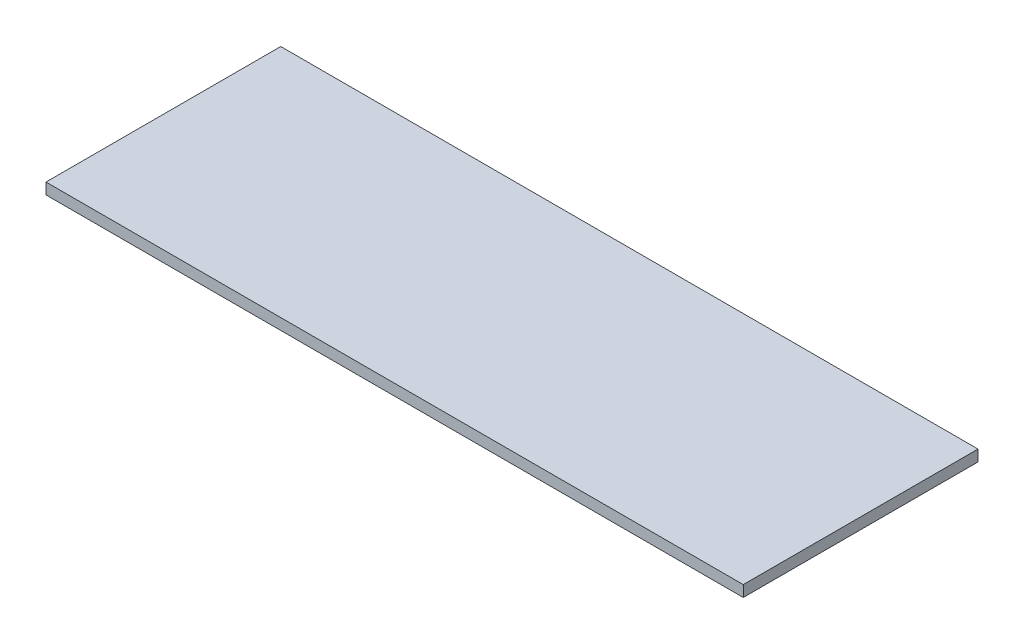
SolidWorks part; units mm, degrees
ref_plane "Front Plane" through (0, 0, 0) normal (0, 0, 1) x (1, 0, 0)
ref_plane "Top Plane" through (0, 0, 0) normal (0, 1, 0) x (1, 0, 0)
ref_plane "Right Plane" through (0, 0, 0) normal (1, 0, 0) x (0, 0, -1)
sketch "Sketch1" plane through (0, 0, 0) normal (0, 1, 0) x (1, 0, 0)
  line L1 (0, 0) -> (1188.1, 0)
  line L2 (0, 0) -> (0, 400)
  line L3 (0, 400) -> (1188.1, 400)
  line L4 (1188.1, 0) -> (1188.1, 400)
  dimension "D1" = 1188.1
  dimension "D2" = 400
extrude "Boss-Extrude1" add sketch "Sketch1" along normal blind 19.05
